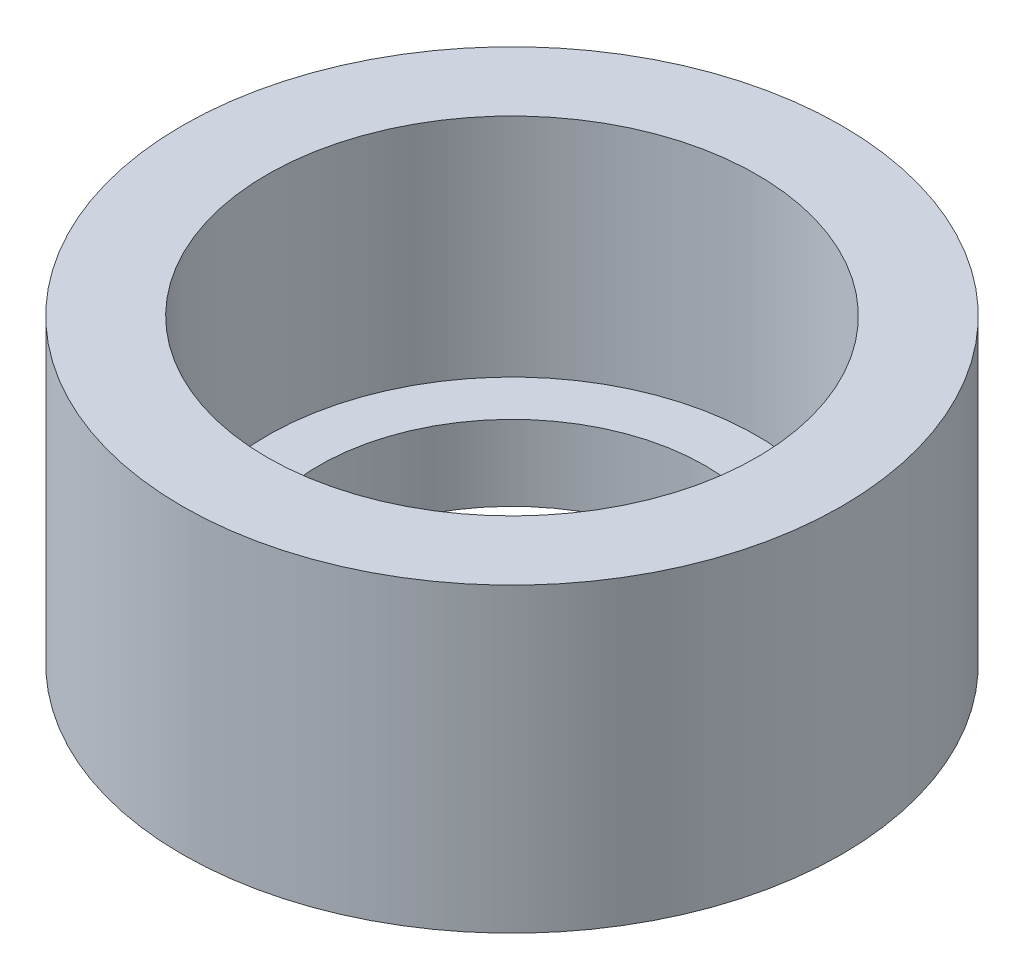
SolidWorks part; units mm, degrees
ref_plane "Front Plane" through (0, 0, 0) normal (0, 0, 1) x (1, 0, 0)
ref_plane "Top Plane" through (0, 0, 0) normal (0, 1, 0) x (1, 0, 0)
ref_plane "Right Plane" through (0, 0, 0) normal (1, 0, 0) x (0, 0, -1)
sketch "Sketch1" plane through (0, 0, 0) normal (0, 1, 0) x (1, 0, 0)
  circle A0 centre (0, 0) radius 8.75
  circle A1 centre (0, 0) radius 5.125
  dimension "D1" = 17.5
  dimension "D2" = 10.25
extrude "Boss-Extrude1" add sketch "Sketch1" along normal blind 8
sketch "Sketch2" plane through (0, 8, 0) normal (0, 1, 0) x (1, 0, 0)
  circle A0 centre (0, 0) radius 6.5
extrude "Cut-Extrude1" cut sketch "Sketch2" against normal blind 6
